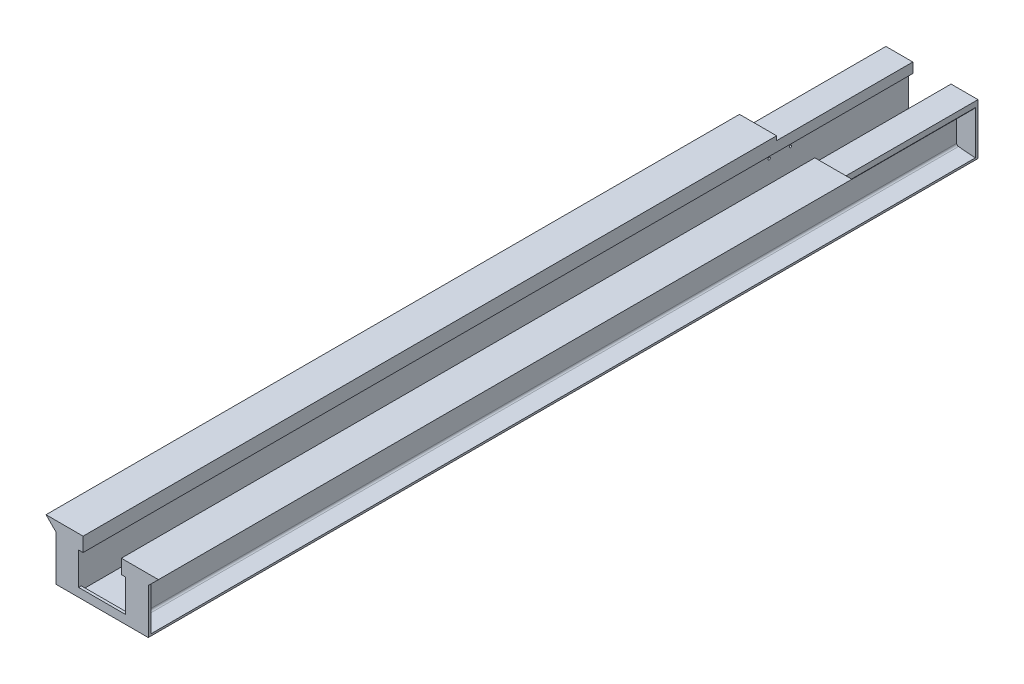
SolidWorks part; units mm, degrees
material "1.5714 (16NiCr4)"
ref_plane "Płaszczyzna przednia" through (0, 0, 0) normal (0, 0, 1) x (1, 0, 0)
ref_plane "Płaszczyzna górna" through (0, 0, 0) normal (0, 1, 0) x (1, 0, 0)
ref_plane "Płaszczyzna prawa" through (0, 0, 0) normal (1, 0, 0) x (0, 0, -1)
sketch "Szkic4" plane through (0, 0, 0) normal (0, 0, 1) x (1, 0, 0)
  line L0 (0, 0) -> (0, 5)
  line L1 (0, 5) -> (48.5, 9)
  line L2 (48.5, 9) -> (48.5, 107)
  line L3 (48.5, 107) -> (6.5, 111)
  line L4 (6.5, 111) -> (-26.5, 144)
  line L5 (-26.5, 144) -> (70.2, 144)
  line L6 (70.2, 144) -> (70.2, 107)
  line L7 (70.2, 107) -> (58.6796, 107)
  line L8 (58.6796, 107) -> (58.6796, 13)
  line L9 (58.6796, 13) -> (181.3, 13)
  line L10 (181.3, 13) -> (181.3, 107)
  line L11 (181.3, 107) -> (169.8, 107)
  line L12 (169.8, 107) -> (169.8, 144)
  line L13 (169.8, 144) -> (266.5, 144)
  line L14 (266.5, 144) -> (233.5, 111)
  line L15 (233.5, 111) -> (191.5, 107)
  line L16 (191.5, 107) -> (191.5, 9)
  line L17 (191.5, 9) -> (240, 5)
  line L18 (240, 5) -> (240, 0)
  line L19 (240, 0) -> (0, 0)
  dimension "D1" = 96.7
  dimension "D2" = 37
  dimension "D3" = 45
  dimension "D4" = 37
  dimension "D5" = 75
  dimension "D6" = 11.5204
  dimension "D7" = 240
  dimension "D8" = 144
  dimension "D9" = 96.7
  dimension "D10" = 99.6
  dimension "D11" = 144
  dimension "D12" = 37
  dimension "D13" = 11.5
  dimension "D14" = 37
  dimension "D15" = 45
  dimension "D16" = 75
  dimension "D17" = 33
  dimension "D18" = 33
  dimension "D19" = 5
  dimension "D20" = 9
  dimension "D21" = 5
  dimension "D22" = 9
  dimension "D23" = 13
  dimension "D24" = 48.5
extrude "Dodanie-wyciągnięcie1" add sketch "Szkic4" along normal blind 1800 contours L5 L6 L7 L8 L9 L10 L11 L12 L13 L14 L15 L16 L17 L18 L19 L0 L1 L2 L3 L4
sketch "Szkic5" plane through (0, 0, 0) normal (0, 0, 1) x (1, 0, 0)
  line L0 (0, 0) -> (0, 5)
  line L1 (0, 5) -> (48.5, 9)
  line L2 (48.5, 9) -> (48.5, 107)
  line L3 (48.5, 107) -> (6.5, 111)
  line L5 (6.5, 133) -> (70.2, 133)
  line L6 (70.2, 133) -> (70.2, 107)
  line L7 (70.2, 107) -> (58.6796, 107)
  line L8 (58.6796, 107) -> (58.6796, 13)
  line L9 (58.6796, 13) -> (181.3, 13)
  line L10 (181.3, 13) -> (181.3, 107)
  line L11 (181.3, 107) -> (169.8, 107)
  line L12 (169.8, 107) -> (169.8, 133)
  line L13 (169.8, 133) -> (233.5, 133)
  line L15 (233.5, 111) -> (191.5, 107)
  line L16 (191.5, 107) -> (191.5, 9)
  line L17 (191.5, 9) -> (240, 5)
  line L18 (240, 5) -> (240, 0)
  line L19 (240, 0) -> (0, 0)
  line L20 (6.5, 111) -> (0, 117.5)
  line L21 (6.5, 111) -> (-26.5, 144) construction
  line L22 (0, 117.5) -> (0, 133)
  line L23 (0, 133) -> (6.5, 133)
  line L24 (233.5, 111) -> (240, 118.3946)
  line L26 (240, 118.3946) -> (240, 133)
  line L27 (240, 133) -> (233.5, 133)
  dimension "D3" = 133
  dimension "D4" = 26
  dimension "D5" = 133
  dimension "D6" = 13
  dimension "D7" = 240
  dimension "D12" = 26
  dimension "D19" = 5
  dimension "D20" = 9
  dimension "D21" = 5
  dimension "D22" = 9
  dimension "D24" = 48.5
extrude "Dodanie-wyciągnięcie2" add sketch "Szkic5" against normal blind 348
sketch "Szkic10" plane through (0, 0, -348) normal (0, 0, 1) x (1, 0, 0)
  line L0 (0, 0) -> (0, 117.5)
  line L5 (6.5, 133) -> (70.2, 133)
  line L6 (70.2, 133) -> (70.2, 107)
  line L7 (70.2, 107) -> (58.6796, 107)
  line L8 (58.6796, 107) -> (58.6796, 22.5)
  line L9 (58.6796, 22.5) -> (181.3, 22.5)
  line L10 (181.3, 22.5) -> (181.3, 107)
  line L11 (181.3, 107) -> (169.8, 107)
  line L12 (169.8, 107) -> (169.8, 133)
  line L13 (169.8, 133) -> (233.5, 133)
  line L18 (240, 118.3946) -> (240, 0)
  line L19 (240, 0) -> (0, 0)
  line L22 (0, 117.5) -> (0, 133)
  line L23 (0, 133) -> (6.5, 133)
  line L26 (240, 118.3946) -> (240, 133)
  line L27 (240, 133) -> (233.5, 133)
  dimension "D3" = 133
  dimension "D4" = 26
  dimension "D5" = 133
  dimension "D7" = 240
  dimension "D12" = 26
  dimension "D23" = 22.5
extrude "Dodanie-wyciągnięcie3" add sketch "Szkic10" against normal blind 7
sketch "Szkic11" plane through (0, 0, 1800) normal (0, 0, 1) x (1, 0, 0)
  line L0 (0, 0) -> (0, 5)
  line L5 (-26.5, 144) -> (70.2, 144)
  line L6 (70.2, 144) -> (70.2, 107)
  line L7 (70.2, 107) -> (58.6796, 107)
  line L8 (58.6796, 107) -> (58.6796, 22.5)
  line L9 (58.6796, 22.5) -> (181.3, 22.5)
  line L10 (181.3, 22.5) -> (181.3, 107)
  line L11 (181.3, 107) -> (169.8, 107)
  line L12 (169.8, 107) -> (169.8, 144)
  line L13 (169.8, 144) -> (266.5, 144)
  line L18 (240, 5) -> (240, 0)
  line L19 (240, 0) -> (0, 0)
  line L20 (-26.5, 144) -> (0, 117.5)
  line L21 (0, 117.5) -> (0, 5)
  line L22 (266.5, 144) -> (240, 117.5)
  line L23 (240, 5) -> (240, 118.3946) construction
  line L24 (266.5, 144) -> (233.5, 111) construction
  line L25 (240, 117.5) -> (240, 5)
  dimension "D1" = 96.7
  dimension "D4" = 37
  dimension "D6" = 11.5204
  dimension "D7" = 240
  dimension "D8" = 144
  dimension "D9" = 96.7
  dimension "D10" = 99.6
  dimension "D11" = 144
  dimension "D12" = 37
  dimension "D13" = 11.5
  dimension "D19" = 5
  dimension "D21" = 5
  dimension "D23" = 22.5
extrude "Dodanie-wyciągnięcie5" add sketch "Szkic11" along normal blind 7
fillet "Zaokrąglenie1" radius 5 4 edges at (191.5, 107, 726) (191.5, 9, 726) (48.5, 107, 726) (48.5, 9, 726)
sketch "Szkic16" plane through (48.5, 0, 0) normal (-1, 0, 0) x (0, 0, 1)
  line L4 (-348, 102.4536) -> (-348, 13.6046) construction
  circle A0 centre (-48, 90.4536) radius 3
  circle A1 centre (7.7, 90.4536) radius 3
  circle A2 centre (7.7, 24.4536) radius 3
  circle A3 centre (-48, 24.4536) radius 3
  dimension "D1" = 55.7
  dimension "D2" = 66
  dimension "D3" = 300
extrude "Wytnij-wyciągnięcie1" cut sketch "Szkic16" against normal blind 10.2
